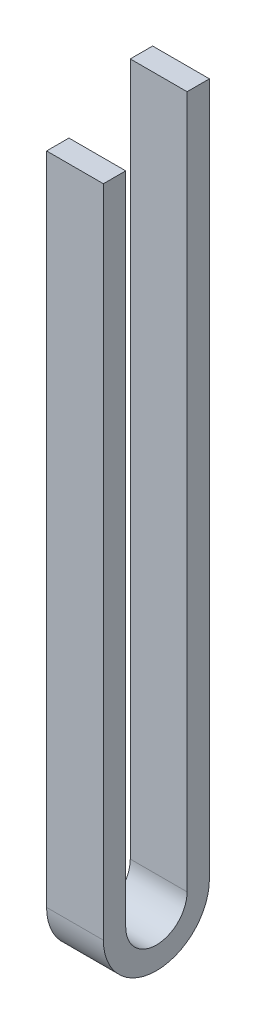
SolidWorks part; units mm, degrees
ref_plane "Front" through (0, 0, 0) normal (0, 0, 1) x (1, 0, 0)
ref_plane "Top" through (0, 0, 0) normal (0, 1, 0) x (1, 0, 0)
ref_plane "Right" through (0, 0, 0) normal (1, 0, 0) x (0, 0, -1)
sketch "Sketch1" plane through (0, 0, 0) normal (1, 0, 0) x (0, 0, -1)
  line L0 (0, 0) -> (0, -439.4425)
  line L1 (71.12, -439.4425) -> (71.12, 25.4)
  line L2 (14.986, 0) -> (14.986, -439.4425)
  line L3 (56.134, -439.4425) -> (56.134, 25.4)
  line L4 (0, 0) -> (14.986, 0)
  line L5 (56.134, 25.4) -> (71.12, 25.4)
  line L6 (23.876, 25.4) -> (145.796, 25.4) construction
  arc A0 (0, -439.4425) -> (71.12, -439.4425) centre (35.56, -439.4425) ccw
  arc A1 (14.986, -439.4425) -> (56.134, -439.4425) centre (35.56, -439.4425) ccw
  dimension "D1" = 1016
  dimension "D2" = 71.12
  dimension "D4" = 41.148
  dimension "D3" = 14.986
extrude "Boss-Extrude1" add sketch "Sketch1" along normal blind 38.1
